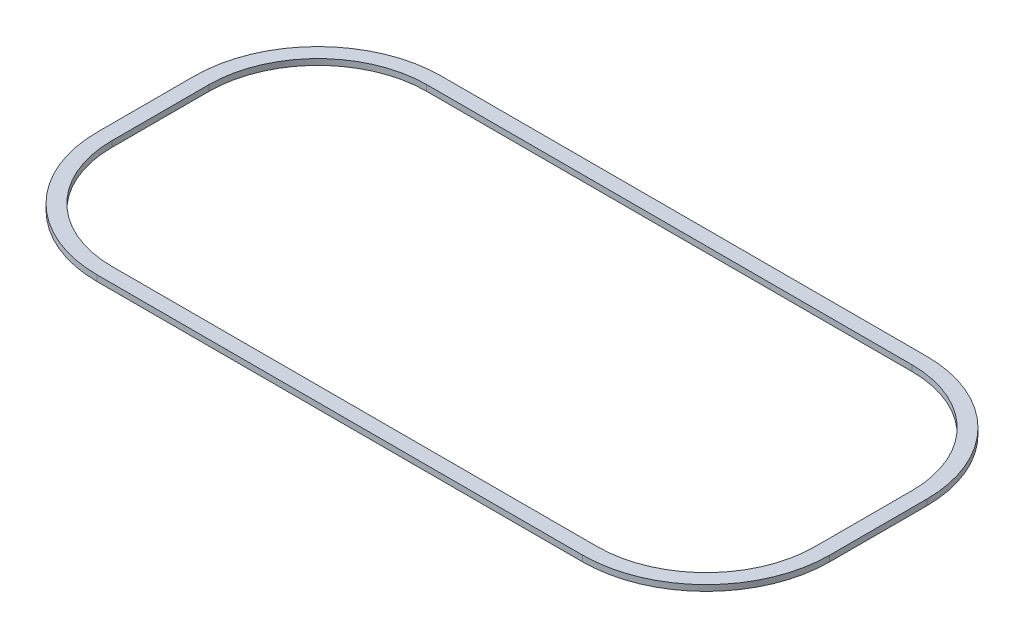
SolidWorks part; units mm, degrees
ref_plane "Front Plane" through (0, 0, 0) normal (0, 0, 1) x (1, 0, 0)
ref_plane "Top Plane" through (0, 0, 0) normal (0, 1, 0) x (1, 0, 0)
ref_plane "Right Plane" through (0, 0, 0) normal (1, 0, 0) x (0, 0, -1)
sketch "Sketch1" plane through (0, 0, 0) normal (0, 1, 0) x (1, 0, 0)
  line L0 (0, 0) -> (83.82, 0)
  line L1 (105.1646, 21.3446) -> (105.1646, 38.1086)
  line L2 (83.82, 59.4532) -> (0, 59.4532)
  line L3 (-21.3446, 38.1086) -> (-21.3446, 21.3446)
  line L4 (0, 2.54) -> (83.82, 2.54)
  line L5 (102.6246, 21.3446) -> (102.6246, 38.1086)
  line L6 (83.82, 56.9132) -> (0, 56.9132)
  line L7 (-18.8046, 38.1086) -> (-18.8046, 21.3446)
  arc A0 (83.82, 0) -> (105.1646, 21.3446) centre (83.82, 21.3446) ccw
  arc A1 (105.1646, 38.1086) -> (83.82, 59.4532) centre (83.82, 38.1086) ccw
  arc A2 (0, 59.4532) -> (-21.3446, 38.1086) centre (0, 38.1086) ccw
  arc A3 (-21.3446, 21.3446) -> (0, 0) centre (0, 21.3446) ccw
  arc A4 (83.82, 2.54) -> (102.6246, 21.3446) centre (83.82, 21.3446) ccw
  arc A5 (102.6246, 38.1086) -> (83.82, 56.9132) centre (83.82, 38.1086) ccw
  arc A6 (0, 56.9132) -> (-18.8046, 38.1086) centre (0, 38.1086) ccw
  arc A7 (-18.8046, 21.3446) -> (0, 2.54) centre (0, 21.3446) ccw
  dimension "D3" = 33.528
  dimension "D4" = 33.528
  dimension "D1" = 83.82
  dimension "D2" = 16.764
  dimension "D5" = 83.82
  dimension "D6" = 33.528
  dimension "D7" = 2.54
extrude "Boss-Extrude1" add sketch "Sketch1" along normal blind 1.016
